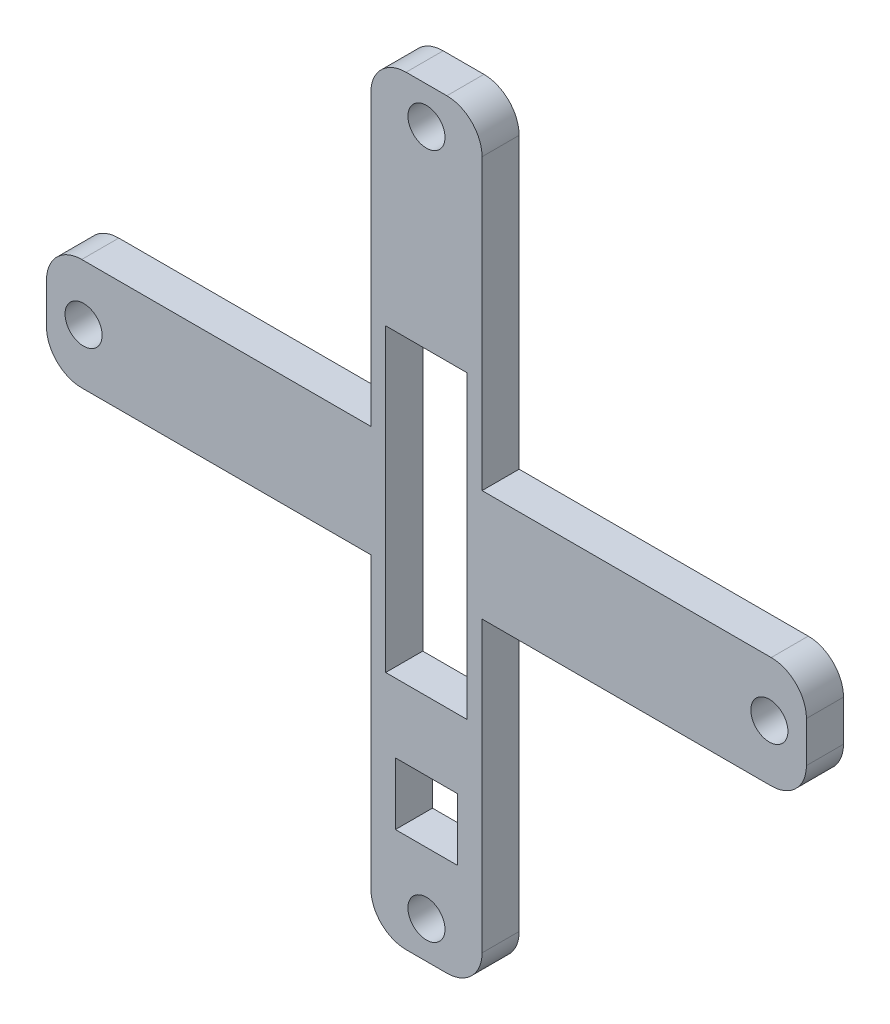
SolidWorks part; units mm, degrees
ref_plane "Alzado" through (0, 0, 0) normal (0, 0, 1) x (1, 0, 0)
ref_plane "Planta" through (0, 0, 0) normal (0, 1, 0) x (1, 0, 0)
ref_plane "Vista lateral" through (0, 0, 0) normal (1, 0, 0) x (0, 0, -1)
sketch "Croquis1" plane through (0, 0, 0) normal (0, 0, 1) x (1, 0, 0)
  line L0 (0, 18.5) -> (0, -18.5) construction
  line L1 (-18.5, 0) -> (18.5, 0) construction
  line L2 (-3, 3) -> (-3, 18.6)
  line L3 (-1.1, 20.5) -> (1.1, 20.5)
  line L4 (3, 18.6) -> (3, 3)
  line L5 (3, 3) -> (18.6, 3)
  line L6 (20.5, 1.1) -> (20.5, -1.1)
  line L7 (18.6, -3) -> (3, -3)
  line L8 (3, -3) -> (3, -18.6)
  line L9 (1.1, -20.5) -> (-1.1, -20.5)
  line L10 (-3, -18.6) -> (-3, -3)
  line L11 (-3, -3) -> (-18.6, -3)
  line L12 (-20.5, -1.1) -> (-20.5, 1.1)
  line L13 (-18.6, 3) -> (-3, 3)
  line L15 (-1.675, -11.825) -> (1.675, -11.825)
  line L16 (-1.675, -11.825) -> (-1.675, -15.175)
  line L17 (-1.675, -15.175) -> (1.675, -15.175)
  line L18 (1.675, -11.825) -> (1.675, -15.175)
  line L19 (-1.675, -11.825) -> (1.675, -15.175) construction
  line L20 (-1.675, -15.175) -> (1.675, -11.825) construction
  line L21 (-2.2, -8.1) -> (2.2, -8.1)
  line L22 (-2.2, -8.1) -> (-2.2, 8.1)
  line L23 (-2.2, 8.1) -> (2.2, 8.1)
  line L24 (2.2, -8.1) -> (2.2, 8.1)
  line L25 (-2.2, -8.1) -> (2.2, 8.1) construction
  line L26 (-2.2, 8.1) -> (2.2, -8.1) construction
  circle A0 centre (0, 18.5) radius 1
  arc A1 (1.1, 20.5) -> (3, 18.6) centre (1.1, 18.6) cw
  arc A2 (-3, 18.6) -> (-1.1, 20.5) centre (-1.1, 18.6) cw
  circle A3 centre (18.5, 0) radius 1
  arc A4 (20.5, -1.1) -> (18.6, -3) centre (18.6, -1.1) cw
  arc A5 (18.6, 3) -> (20.5, 1.1) centre (18.6, 1.1) cw
  circle A6 centre (0, -18.5) radius 1
  arc A7 (-1.1, -20.5) -> (-3, -18.6) centre (-1.1, -18.6) cw
  arc A8 (3, -18.6) -> (1.1, -20.5) centre (1.1, -18.6) cw
  circle A9 centre (-18.5, 0) radius 1
  arc A10 (-20.5, 1.1) -> (-18.6, 3) centre (-18.6, 1.1) cw
  arc A11 (-18.6, -3) -> (-20.5, -1.1) centre (-18.6, -1.1) cw
  point P3 (0, 0)
  point P6 (0, 0)
  point P11 (0, -13.5)
  point P41 (0, 0)
  dimension "D3" = 2
  dimension "D8" = 1.9
  dimension "D1" = 37
  dimension "D2" = 37
  dimension "D4" = 6
  dimension "D5" = 3
  dimension "D6" = 2
  dimension "D7" = 3
  dimension "D10" = 3.35
  dimension "D11" = 3.35
  dimension "D12" = 5
  dimension "D13" = 4.4
  dimension "D14" = 16.2
  dimension "D9" = 4
extrude "Saliente-Extruir1" add sketch "Croquis1" along normal blind 2
